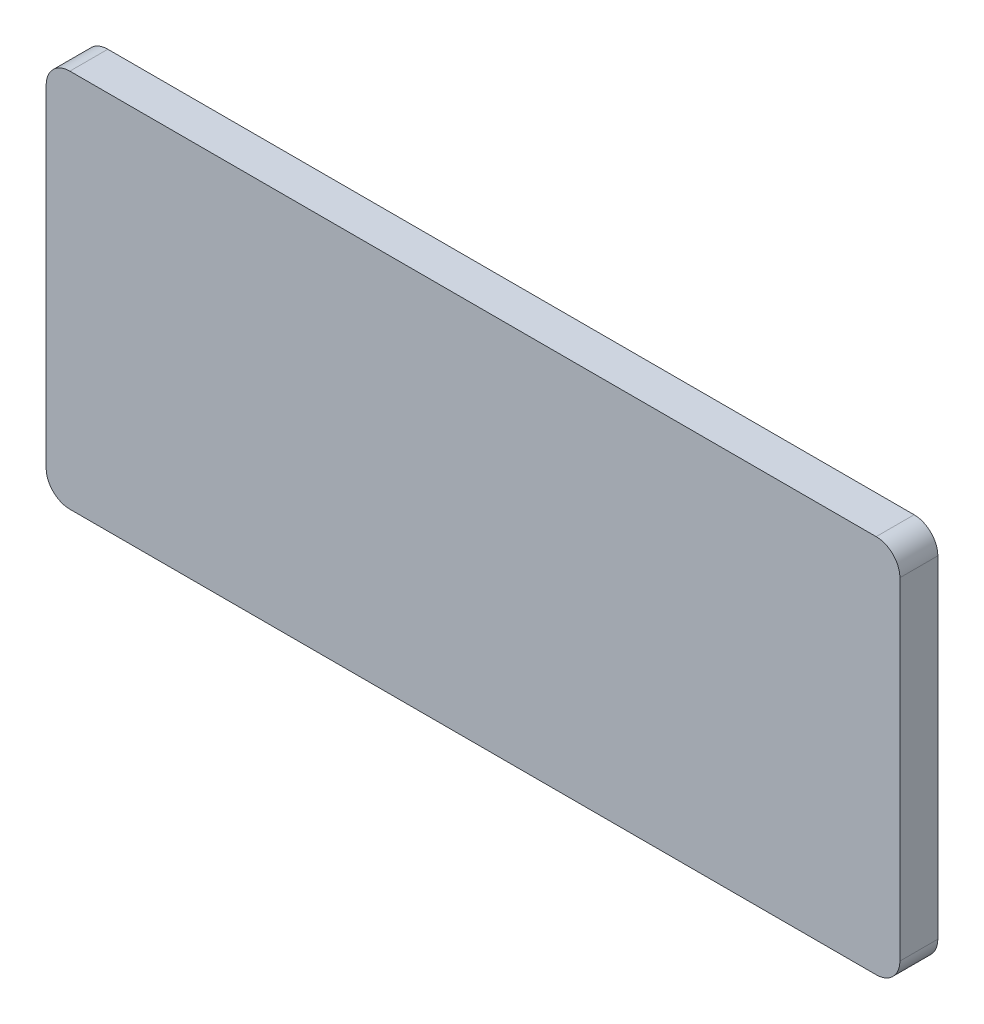
SolidWorks part; units mm, degrees
ref_plane "前视基准面" through (0, 0, 0) normal (0, 0, 1) x (1, 0, 0)
ref_plane "上视基准面" through (0, 0, 0) normal (0, 1, 0) x (1, 0, 0)
ref_plane "右视基准面" through (0, 0, 0) normal (1, 0, 0) x (0, 0, -1)
sketch "草图1" plane through (0, 0, 0) normal (0, 0, 1) x (1, 0, 0)
  line L1 (-17, 8) -> (17, 8)
  line L2 (-18, 7) -> (-18, -7)
  line L3 (-17, -8) -> (17, -8)
  line L4 (18, 7) -> (18, -7)
  line L5 (-18, 8) -> (18, -8) construction
  line L6 (-18, -8) -> (18, 8) construction
  arc A0 (17, 8) -> (18, 7) centre (17, 7) cw
  arc A1 (18, -7) -> (17, -8) centre (17, -7) cw
  arc A2 (-17, -8) -> (-18, -7) centre (-17, -7) cw
  arc A3 (-18, 7) -> (-17, 8) centre (-17, 7) cw
  point P0 (0, 0)
  dimension "D3" = 1
  dimension "D1" = 36
  dimension "D2" = 16
extrude "凸台-拉伸1" add sketch "草图1" along normal blind 1.6
